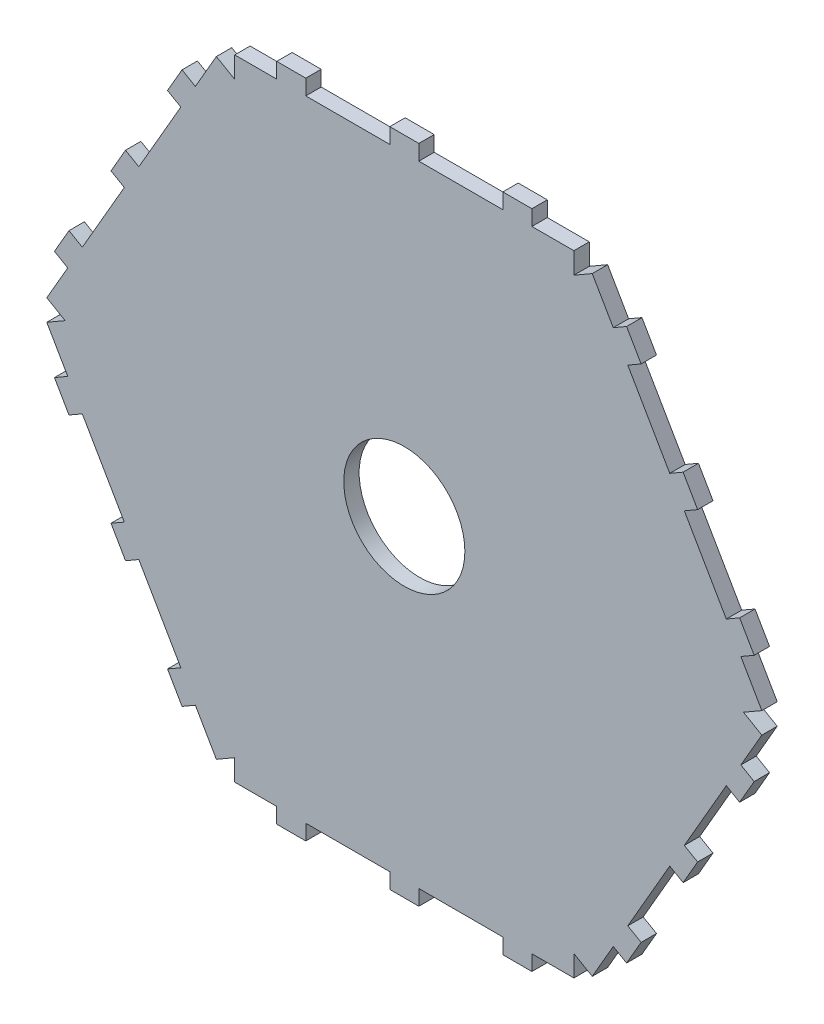
SolidWorks part; units mm, degrees
ref_plane "Front Plane" through (0, 0, 0) normal (0, 0, 1) x (1, 0, 0)
ref_plane "Top Plane" through (0, 0, 0) normal (0, 1, 0) x (1, 0, 0)
ref_plane "Right Plane" through (0, 0, 0) normal (1, 0, 0) x (0, 0, -1)
sketch "Sketch2" plane through (0, 0, 0) normal (0, 0, 1) x (1, 0, 0)
  line L0 (-35, 65) -> (-35, 60.6218)
  line L1 (35, 65) -> (35, 60.6218)
  line L2 (-35, 65) -> (-11.6667, 65) construction
  line L3 (-35, 60.6218) -> (35, 60.6218) construction
  line L4 (35, 60.6218) -> (70, 0) construction
  line L5 (70, 0) -> (35, -60.6218) construction
  line L6 (35, -60.6218) -> (-35, -60.6218) construction
  line L7 (0, 87.3633) -> (0, -0.0109) construction
  line L8 (0, 0) -> (44.1971, 0) construction
  line L9 (-11.6667, 65) -> (11.6667, 65) construction
  line L10 (11.6667, 65) -> (35, 65) construction
  line L11 (-23.3333, 65) -> (-23.3333, 68.175) construction
  line L12 (-20.3333, 68.175) -> (-26.3333, 68.175)
  line L13 (-35, -60.6218) -> (-70, 0) construction
  line L14 (-70, 0) -> (-35, 60.6218) construction
  line L15 (-70, 0) -> (59.0387, 0)
  line L16 (-26.3333, 68.175) -> (-26.3333, 65)
  line L17 (-26.3333, 68.175) -> (-20.3333, 68.175)
  line L18 (-20.3333, 68.175) -> (-20.3333, 65)
  line L19 (-11.6667, 137.7104) -> (-11.6667, 152.546) construction
  line L20 (11.6667, 137.7104) -> (11.6667, 152.546) construction
  line L21 (-26.3333, 68.175) -> (-26.3333, 65)
  line L22 (-20.3333, 68.175) -> (-20.3333, 65)
  line L23 (-26.3333, 68.175) -> (-26.3333, 65)
  line L24 (-20.3333, 68.175) -> (-20.3333, 65)
  line L25 (-26.3333, 68.175) -> (-26.3333, 65)
  line L26 (-20.3333, 68.175) -> (-20.3333, 65)
  line L27 (-26.3333, 68.175) -> (-26.3333, 65)
  line L28 (-20.3333, 68.175) -> (-20.3333, 65)
  line L29 (-26.3333, 68.175) -> (-26.3333, 65)
  line L30 (-20.3333, 68.175) -> (-20.3333, 65)
  line L31 (-26.3333, 68.175) -> (-26.3333, 65)
  line L32 (-20.3333, 68.175) -> (-20.3333, 65)
  line L33 (-26.3333, 68.175) -> (-26.3333, 65)
  line L34 (-20.3333, 68.175) -> (-20.3333, 65)
  line L35 (-26.3333, 68.175) -> (-26.3333, 65)
  line L36 (-20.3333, 68.175) -> (-20.3333, 65)
  line L37 (-26.3333, 68.175) -> (-26.3333, 65)
  line L38 (-20.3333, 68.175) -> (-20.3333, 65)
  line L39 (-26.3333, 68.175) -> (-26.3333, 65)
  line L40 (-20.3333, 68.175) -> (-20.3333, 65)
  line L41 (-26.3333, 68.175) -> (-26.3333, 65)
  line L42 (-20.3333, 68.175) -> (-20.3333, 65)
  line L43 (-26.3333, 68.175) -> (-26.3333, 65)
  line L44 (-20.3333, 68.175) -> (-20.3333, 65)
  line L45 (-26.3333, 68.175) -> (-26.3333, 65)
  line L46 (-20.3333, 68.175) -> (-20.3333, 65)
  line L47 (-26.3333, 68.175) -> (-26.3333, 65)
  line L48 (-20.3333, 68.175) -> (-20.3333, 65)
  line L49 (-26.3333, 68.175) -> (-26.3333, 65)
  line L50 (-20.3333, 68.175) -> (-20.3333, 65)
  line L51 (-26.3333, 68.175) -> (-26.3333, 65)
  line L52 (-20.3333, 68.175) -> (-20.3333, 65)
  line L53 (-26.3333, 68.175) -> (-26.3333, 65)
  line L54 (-20.3333, 68.175) -> (-20.3333, 65)
  line L55 (-26.3333, 68.175) -> (-26.3333, 65)
  line L56 (-20.3333, 68.175) -> (-20.3333, 65)
  line L57 (-26.3333, 68.175) -> (-26.3333, 65)
  line L58 (-20.3333, 68.175) -> (-20.3333, 65)
  line L59 (-26.3333, 68.175) -> (-26.3333, 65)
  line L60 (-20.3333, 68.175) -> (-20.3333, 65)
  line L61 (-26.3333, 68.175) -> (-26.3333, 65)
  line L62 (-20.3333, 68.175) -> (-20.3333, 65)
  line L63 (-26.3333, 68.175) -> (-26.3333, 65)
  line L64 (-20.3333, 68.175) -> (-20.3333, 65)
  line L65 (-26.3333, 68.175) -> (-26.3333, 65)
  line L66 (-20.3333, 68.175) -> (-20.3333, 65)
  line L67 (-26.3333, 68.175) -> (-26.3333, 65)
  line L68 (-20.3333, 68.175) -> (-20.3333, 65)
  line L69 (-26.3333, 68.175) -> (-26.3333, 65)
  line L70 (-20.3333, 68.175) -> (-20.3333, 65)
  line L71 (-26.3333, 68.175) -> (-26.3333, 65)
  line L72 (-20.3333, 68.175) -> (-20.3333, 65)
  line L73 (-26.3333, 68.175) -> (-26.3333, 65)
  line L74 (-20.3333, 68.175) -> (-20.3333, 65)
  line L75 (-26.3333, 68.175) -> (-26.3333, 65)
  line L76 (-20.3333, 68.175) -> (-20.3333, 65)
  line L77 (-26.3333, 68.175) -> (-26.3333, 65)
  line L78 (-20.3333, 68.175) -> (-20.3333, 65)
  line L79 (-26.3333, 68.175) -> (-26.3333, 65)
  line L80 (-20.3333, 68.175) -> (-20.3333, 65)
  line L81 (-26.3333, 68.175) -> (-26.3333, 65)
  line L82 (-20.3333, 68.175) -> (-20.3333, 65)
  line L83 (0, 65) -> (0, 68.175) construction
  line L84 (-3, 68.175) -> (-3, 65)
  line L85 (3, 68.175) -> (3, 65)
  line L86 (-3, 68.175) -> (-3, 65)
  line L87 (3, 68.175) -> (3, 65)
  line L88 (-3, 68.175) -> (-3, 65)
  line L89 (3, 68.175) -> (3, 65)
  line L90 (-3, 68.175) -> (-3, 65)
  line L91 (3, 68.175) -> (3, 65)
  line L92 (-3, 68.175) -> (-3, 65)
  line L93 (3, 68.175) -> (3, 65)
  line L94 (-3, 68.175) -> (-3, 65)
  line L95 (3, 68.175) -> (3, 65)
  line L96 (-3, 68.175) -> (-3, 65)
  line L97 (3, 68.175) -> (3, 65)
  line L98 (-3, 68.175) -> (-3, 65)
  line L99 (3, 68.175) -> (3, 65)
  line L100 (-3, 68.175) -> (-3, 65)
  line L101 (3, 68.175) -> (3, 65)
  line L102 (-3, 68.175) -> (-3, 65)
  line L103 (3, 68.175) -> (3, 65)
  line L104 (-3, 68.175) -> (-3, 65)
  line L105 (3, 68.175) -> (3, 65)
  line L106 (-3, 68.175) -> (-3, 65)
  line L107 (3, 68.175) -> (3, 65)
  line L108 (-3, 68.175) -> (-3, 65)
  line L109 (3, 68.175) -> (3, 65)
  line L110 (-3, 68.175) -> (-3, 65)
  line L111 (3, 68.175) -> (3, 65)
  line L112 (-3, 68.175) -> (-3, 65)
  line L113 (3, 68.175) -> (3, 65)
  line L114 (-3, 68.175) -> (-3, 65)
  line L115 (3, 68.175) -> (3, 65)
  line L116 (-3, 68.175) -> (-3, 65)
  line L117 (3, 68.175) -> (3, 65)
  line L118 (-3, 68.175) -> (-3, 65)
  line L119 (3, 68.175) -> (3, 65)
  line L120 (-3, 68.175) -> (-3, 65)
  line L121 (3, 68.175) -> (3, 65)
  line L122 (-3, 68.175) -> (-3, 65)
  line L123 (3, 68.175) -> (3, 65)
  line L124 (-3, 68.175) -> (-3, 65)
  line L125 (3, 68.175) -> (3, 65)
  line L126 (-3, 68.175) -> (-3, 65)
  line L127 (3, 68.175) -> (3, 65)
  line L128 (-3, 68.175) -> (-3, 65)
  line L129 (3, 68.175) -> (3, 65)
  line L130 (-3, 68.175) -> (-3, 65)
  line L131 (3, 68.175) -> (3, 65)
  line L132 (-3, 68.175) -> (-3, 65)
  line L133 (3, 68.175) -> (3, 65)
  line L134 (-3, 68.175) -> (-3, 65)
  line L135 (3, 68.175) -> (3, 65)
  line L136 (-3, 68.175) -> (-3, 65)
  line L137 (3, 68.175) -> (3, 65)
  line L138 (-3, 68.175) -> (-3, 65)
  line L139 (3, 68.175) -> (3, 65)
  line L140 (-3, 68.175) -> (-3, 65)
  line L141 (3, 68.175) -> (3, 65)
  line L142 (-3, 68.175) -> (-3, 65)
  line L143 (3, 68.175) -> (3, 65)
  line L144 (-3, 68.175) -> (-3, 65)
  line L145 (3, 68.175) -> (3, 65)
  line L146 (-3, 68.175) -> (-3, 65)
  line L147 (3, 68.175) -> (-3, 68.175)
  line L148 (3, 68.175) -> (3, 65)
  line L149 (-3, 68.175) -> (3, 68.175)
  line L150 (-3, 68.175) -> (-3, 65)
  line L151 (3, 68.175) -> (3, 65)
  line L152 (-3, 68.175) -> (-3, 65)
  line L153 (3, 68.175) -> (3, 65)
  line L154 (-3, 68.175) -> (-3, 65)
  line L155 (3, 68.175) -> (3, 65)
  line L156 (-3, 68.175) -> (-3, 65)
  line L157 (3, 68.175) -> (3, 65)
  line L158 (-3, 68.175) -> (-3, 65)
  line L159 (3, 68.175) -> (3, 65)
  line L160 (-3, 68.175) -> (-3, 65)
  line L161 (3, 68.175) -> (3, 65)
  line L162 (-3, 68.175) -> (-3, 65)
  line L163 (3, 68.175) -> (3, 65)
  line L164 (-3, 68.175) -> (-3, 65)
  line L165 (3, 68.175) -> (3, 65)
  line L166 (-3, 68.175) -> (-3, 65)
  line L167 (3, 68.175) -> (3, 65)
  line L168 (-3, 68.175) -> (-3, 65)
  line L169 (3, 68.175) -> (3, 65)
  line L170 (-3, 68.175) -> (-3, 65)
  line L171 (3, 68.175) -> (3, 65)
  line L172 (-3, 68.175) -> (-3, 65)
  line L173 (3, 68.175) -> (3, 65)
  line L174 (-3, 68.175) -> (-3, 65)
  line L175 (3, 68.175) -> (3, 65)
  line L176 (-3, 68.175) -> (-3, 65)
  line L177 (3, 68.175) -> (3, 65)
  line L178 (-3, 68.175) -> (-3, 65)
  line L179 (3, 68.175) -> (3, 65)
  line L180 (-3, 68.175) -> (-3, 65)
  line L181 (3, 68.175) -> (3, 65)
  line L182 (-3, 68.175) -> (-3, 65)
  line L183 (3, 68.175) -> (3, 65)
  line L184 (-3, 68.175) -> (-3, 65)
  line L185 (3, 68.175) -> (3, 65)
  line L186 (-3, 68.175) -> (-3, 65)
  line L187 (3, 68.175) -> (3, 65)
  line L188 (-3, 68.175) -> (-3, 65)
  line L189 (3, 68.175) -> (3, 65)
  line L190 (-3, 68.175) -> (-3, 65)
  line L191 (3, 68.175) -> (3, 65)
  line L192 (-3, 68.175) -> (-3, 65)
  line L193 (3, 68.175) -> (3, 65)
  line L194 (-3, 68.175) -> (-3, 65)
  line L195 (3, 68.175) -> (3, 65)
  line L196 (-3, 68.175) -> (-3, 65)
  line L197 (3, 68.175) -> (3, 65)
  line L198 (-3, 68.175) -> (-3, 65)
  line L199 (3, 68.175) -> (3, 65)
  line L200 (-3, 68.175) -> (-3, 65)
  line L201 (3, 68.175) -> (3, 65)
  line L202 (-3, 68.175) -> (-3, 65)
  line L203 (3, 68.175) -> (3, 65)
  line L204 (-3, 68.175) -> (-3, 65)
  line L205 (3, 68.175) -> (3, 65)
  line L206 (-3, 68.175) -> (-3, 65)
  line L207 (3, 68.175) -> (3, 65)
  line L208 (-3, 68.175) -> (-3, 65)
  line L209 (3, 68.175) -> (3, 65)
  line L210 (-3, 68.175) -> (-3, 65)
  line L211 (3, 68.175) -> (3, 65)
  line L212 (-3, 68.175) -> (-3, 65)
  line L213 (3, 68.175) -> (3, 65)
  line L214 (23.3333, 65) -> (23.3333, 68.175) construction
  line L215 (20.3333, 68.175) -> (20.3333, 65)
  line L216 (26.3333, 68.175) -> (26.3333, 65)
  line L217 (20.3333, 68.175) -> (20.3333, 65)
  line L218 (26.3333, 68.175) -> (26.3333, 65)
  line L219 (20.3333, 68.175) -> (20.3333, 65)
  line L220 (26.3333, 68.175) -> (26.3333, 65)
  line L221 (20.3333, 68.175) -> (20.3333, 65)
  line L222 (26.3333, 68.175) -> (26.3333, 65)
  line L223 (20.3333, 68.175) -> (20.3333, 65)
  line L224 (26.3333, 68.175) -> (26.3333, 65)
  line L225 (20.3333, 68.175) -> (20.3333, 65)
  line L226 (26.3333, 68.175) -> (26.3333, 65)
  line L227 (20.3333, 68.175) -> (20.3333, 65)
  line L228 (26.3333, 68.175) -> (26.3333, 65)
  line L229 (20.3333, 68.175) -> (20.3333, 65)
  line L230 (26.3333, 68.175) -> (26.3333, 65)
  line L231 (20.3333, 68.175) -> (20.3333, 65)
  line L232 (26.3333, 68.175) -> (26.3333, 65)
  line L233 (20.3333, 68.175) -> (20.3333, 65)
  line L234 (26.3333, 68.175) -> (26.3333, 65)
  line L235 (20.3333, 68.175) -> (20.3333, 65)
  line L236 (26.3333, 68.175) -> (26.3333, 65)
  line L237 (20.3333, 68.175) -> (20.3333, 65)
  line L238 (26.3333, 68.175) -> (26.3333, 65)
  line L239 (20.3333, 68.175) -> (20.3333, 65)
  line L240 (26.3333, 68.175) -> (26.3333, 65)
  line L241 (20.3333, 68.175) -> (20.3333, 65)
  line L242 (26.3333, 68.175) -> (26.3333, 65)
  line L243 (20.3333, 68.175) -> (20.3333, 65)
  line L244 (26.3333, 68.175) -> (26.3333, 65)
  line L245 (20.3333, 68.175) -> (20.3333, 65)
  line L246 (26.3333, 68.175) -> (26.3333, 65)
  line L247 (20.3333, 68.175) -> (20.3333, 65)
  line L248 (26.3333, 68.175) -> (26.3333, 65)
  line L249 (20.3333, 68.175) -> (20.3333, 65)
  line L250 (26.3333, 68.175) -> (26.3333, 65)
  line L251 (20.3333, 68.175) -> (20.3333, 65)
  line L252 (26.3333, 68.175) -> (26.3333, 65)
  line L253 (20.3333, 68.175) -> (20.3333, 65)
  line L254 (26.3333, 68.175) -> (26.3333, 65)
  line L255 (20.3333, 68.175) -> (20.3333, 65)
  line L256 (26.3333, 68.175) -> (26.3333, 65)
  line L257 (20.3333, 68.175) -> (20.3333, 65)
  line L258 (26.3333, 68.175) -> (26.3333, 65)
  line L259 (20.3333, 68.175) -> (20.3333, 65)
  line L260 (26.3333, 68.175) -> (26.3333, 65)
  line L261 (20.3333, 68.175) -> (20.3333, 65)
  line L262 (26.3333, 68.175) -> (26.3333, 65)
  line L263 (20.3333, 68.175) -> (20.3333, 65)
  line L264 (26.3333, 68.175) -> (26.3333, 65)
  line L265 (20.3333, 68.175) -> (20.3333, 65)
  line L266 (26.3333, 68.175) -> (26.3333, 65)
  line L267 (20.3333, 68.175) -> (20.3333, 65)
  line L268 (26.3333, 68.175) -> (26.3333, 65)
  line L269 (20.3333, 68.175) -> (20.3333, 65)
  line L270 (26.3333, 68.175) -> (26.3333, 65)
  line L271 (20.3333, 68.175) -> (20.3333, 65)
  line L272 (26.3333, 68.175) -> (26.3333, 65)
  line L273 (20.3333, 68.175) -> (20.3333, 65)
  line L274 (26.3333, 68.175) -> (26.3333, 65)
  line L275 (20.3333, 68.175) -> (20.3333, 65)
  line L276 (26.3333, 68.175) -> (26.3333, 65)
  line L277 (20.3333, 68.175) -> (20.3333, 65)
  line L278 (26.3333, 68.175) -> (26.3333, 65)
  line L279 (26.3333, 68.175) -> (20.3333, 68.175)
  line L280 (20.3333, 68.175) -> (20.3333, 65)
  line L281 (20.3333, 68.175) -> (26.3333, 68.175)
  line L282 (26.3333, 68.175) -> (26.3333, 65)
  line L283 (20.3333, 68.175) -> (20.3333, 65)
  line L284 (26.3333, 68.175) -> (26.3333, 65)
  line L285 (20.3333, 68.175) -> (20.3333, 65)
  line L286 (26.3333, 68.175) -> (26.3333, 65)
  line L287 (20.3333, 68.175) -> (20.3333, 65)
  line L288 (26.3333, 68.175) -> (26.3333, 65)
  line L289 (20.3333, 68.175) -> (20.3333, 65)
  line L290 (26.3333, 68.175) -> (26.3333, 65)
  line L291 (20.3333, 68.175) -> (20.3333, 65)
  line L292 (26.3333, 68.175) -> (26.3333, 65)
  line L293 (20.3333, 68.175) -> (20.3333, 65)
  line L294 (26.3333, 68.175) -> (26.3333, 65)
  line L295 (20.3333, 68.175) -> (20.3333, 65)
  line L296 (26.3333, 68.175) -> (26.3333, 65)
  line L297 (20.3333, 68.175) -> (20.3333, 65)
  line L298 (26.3333, 68.175) -> (26.3333, 65)
  line L299 (20.3333, 68.175) -> (20.3333, 65)
  line L300 (26.3333, 68.175) -> (26.3333, 65)
  line L301 (20.3333, 68.175) -> (20.3333, 65)
  line L302 (26.3333, 68.175) -> (26.3333, 65)
  line L303 (20.3333, 68.175) -> (20.3333, 65)
  line L304 (26.3333, 68.175) -> (26.3333, 65)
  line L305 (20.3333, 68.175) -> (20.3333, 65)
  line L306 (26.3333, 68.175) -> (26.3333, 65)
  line L307 (20.3333, 68.175) -> (20.3333, 65)
  line L308 (26.3333, 68.175) -> (26.3333, 65)
  line L309 (20.3333, 68.175) -> (20.3333, 65)
  line L310 (26.3333, 68.175) -> (26.3333, 65)
  line L311 (20.3333, 68.175) -> (20.3333, 65)
  line L312 (26.3333, 68.175) -> (26.3333, 65)
  line L313 (20.3333, 68.175) -> (20.3333, 65)
  line L314 (26.3333, 68.175) -> (26.3333, 65)
  line L315 (20.3333, 68.175) -> (20.3333, 65)
  line L316 (26.3333, 68.175) -> (26.3333, 65)
  line L317 (20.3333, 68.175) -> (20.3333, 65)
  line L318 (26.3333, 68.175) -> (26.3333, 65)
  line L319 (20.3333, 68.175) -> (20.3333, 65)
  line L320 (26.3333, 68.175) -> (26.3333, 65)
  line L321 (20.3333, 68.175) -> (20.3333, 65)
  line L322 (26.3333, 68.175) -> (26.3333, 65)
  line L323 (20.3333, 68.175) -> (20.3333, 65)
  line L324 (26.3333, 68.175) -> (26.3333, 65)
  line L325 (20.3333, 68.175) -> (20.3333, 65)
  line L326 (26.3333, 68.175) -> (26.3333, 65)
  line L327 (20.3333, 68.175) -> (20.3333, 65)
  line L328 (26.3333, 68.175) -> (26.3333, 65)
  line L329 (20.3333, 68.175) -> (20.3333, 65)
  line L330 (26.3333, 68.175) -> (26.3333, 65)
  line L331 (20.3333, 68.175) -> (20.3333, 65)
  line L332 (26.3333, 68.175) -> (26.3333, 65)
  line L333 (20.3333, 68.175) -> (20.3333, 65)
  line L334 (26.3333, 68.175) -> (26.3333, 65)
  line L335 (20.3333, 68.175) -> (20.3333, 65)
  line L336 (26.3333, 68.175) -> (26.3333, 65)
  line L337 (20.3333, 68.175) -> (20.3333, 65)
  line L338 (26.3333, 68.175) -> (26.3333, 65)
  line L339 (20.3333, 68.175) -> (20.3333, 65)
  line L340 (26.3333, 68.175) -> (26.3333, 65)
  line L341 (20.3333, 68.175) -> (20.3333, 65)
  line L342 (26.3333, 68.175) -> (26.3333, 65)
  line L343 (20.3333, 68.175) -> (20.3333, 65)
  line L344 (26.3333, 68.175) -> (26.3333, 65)
  line L345 (-35, 65) -> (-26.3333, 65)
  line L346 (-20.3333, 65) -> (-3, 65)
  line L347 (3, 65) -> (20.3333, 65)
  line L348 (26.3333, 65) -> (35, 65)
  line L349 (45.8746, 56.8928) -> (43.125, 55.3053)
  line L350 (48.8746, 51.6967) -> (45.8746, 56.8928)
  line L351 (48.8746, 51.6967) -> (46.125, 50.1092)
  line L352 (46.125, 50.1092) -> (54.7917, 35.0981)
  line L353 (57.5413, 36.6856) -> (54.7917, 35.0981)
  line L354 (60.5413, 31.4894) -> (57.5413, 36.6856)
  line L355 (60.5413, 31.4894) -> (57.7917, 29.9019)
  line L356 (57.7917, 29.9019) -> (66.4583, 14.8908)
  line L357 (69.2079, 16.4783) -> (66.4583, 14.8908)
  line L358 (72.2079, 11.2822) -> (69.2079, 16.4783)
  line L359 (72.2079, 11.2822) -> (69.4583, 9.6947)
  line L360 (69.4583, 9.6947) -> (73.7917, 2.1891)
  line L361 (38.7917, 62.8109) -> (43.125, 55.3053)
  line L362 (38.7917, 62.8109) -> (35, 60.6218)
  line L363 (73.7917, 2.1891) -> (70, 0)
  line L364 (72.2079, -11.2822) -> (69.4583, -9.6947)
  line L365 (69.2079, -16.4783) -> (72.2079, -11.2822)
  line L366 (69.2079, -16.4783) -> (66.4583, -14.8908)
  line L367 (66.4583, -14.8908) -> (57.7917, -29.9019)
  line L368 (60.5413, -31.4894) -> (57.7917, -29.9019)
  line L369 (57.5413, -36.6856) -> (60.5413, -31.4894)
  line L370 (57.5413, -36.6856) -> (54.7917, -35.0981)
  line L371 (54.7917, -35.0981) -> (46.125, -50.1092)
  line L372 (48.8746, -51.6967) -> (46.125, -50.1092)
  line L373 (45.8746, -56.8928) -> (48.8746, -51.6967)
  line L374 (45.8746, -56.8928) -> (43.125, -55.3053)
  line L375 (43.125, -55.3053) -> (38.7917, -62.8109)
  line L376 (73.7917, -2.1891) -> (69.4583, -9.6947)
  line L377 (73.7917, -2.1891) -> (70, 0)
  line L378 (38.7917, -62.8109) -> (35, -60.6218)
  line L379 (26.3333, -68.175) -> (26.3333, -65)
  line L380 (20.3333, -68.175) -> (26.3333, -68.175)
  line L381 (20.3333, -68.175) -> (20.3333, -65)
  line L382 (20.3333, -65) -> (3, -65)
  line L383 (3, -68.175) -> (3, -65)
  line L384 (-3, -68.175) -> (3, -68.175)
  line L385 (-3, -68.175) -> (-3, -65)
  line L386 (-3, -65) -> (-20.3333, -65)
  line L387 (-20.3333, -68.175) -> (-20.3333, -65)
  line L388 (-26.3333, -68.175) -> (-20.3333, -68.175)
  line L389 (-26.3333, -68.175) -> (-26.3333, -65)
  line L390 (-26.3333, -65) -> (-35, -65)
  line L391 (35, -65) -> (26.3333, -65)
  line L392 (35, -65) -> (35, -60.6218)
  line L393 (-35, -65) -> (-35, -60.6218)
  line L394 (-45.8746, -56.8928) -> (-43.125, -55.3053)
  line L395 (-48.8746, -51.6967) -> (-45.8746, -56.8928)
  line L396 (-48.8746, -51.6967) -> (-46.125, -50.1092)
  line L397 (-46.125, -50.1092) -> (-54.7917, -35.0981)
  line L398 (-57.5413, -36.6856) -> (-54.7917, -35.0981)
  line L399 (-60.5413, -31.4894) -> (-57.5413, -36.6856)
  line L400 (-60.5413, -31.4894) -> (-57.7917, -29.9019)
  line L401 (-57.7917, -29.9019) -> (-66.4583, -14.8908)
  line L402 (-69.2079, -16.4783) -> (-66.4583, -14.8908)
  line L403 (-72.2079, -11.2822) -> (-69.2079, -16.4783)
  line L404 (-72.2079, -11.2822) -> (-69.4583, -9.6947)
  line L405 (-69.4583, -9.6947) -> (-73.7917, -2.1891)
  line L406 (-38.7917, -62.8109) -> (-43.125, -55.3053)
  line L407 (-38.7917, -62.8109) -> (-35, -60.6218)
  line L408 (-73.7917, -2.1891) -> (-70, 0)
  line L409 (-72.2079, 11.2822) -> (-69.4583, 9.6947)
  line L410 (-69.2079, 16.4783) -> (-72.2079, 11.2822)
  line L411 (-69.2079, 16.4783) -> (-66.4583, 14.8908)
  line L412 (-66.4583, 14.8908) -> (-57.7917, 29.9019)
  line L413 (-60.5413, 31.4894) -> (-57.7917, 29.9019)
  line L414 (-57.5413, 36.6856) -> (-60.5413, 31.4894)
  line L415 (-57.5413, 36.6856) -> (-54.7917, 35.0981)
  line L416 (-54.7917, 35.0981) -> (-46.125, 50.1092)
  line L417 (-48.8746, 51.6967) -> (-46.125, 50.1092)
  line L418 (-45.8746, 56.8928) -> (-48.8746, 51.6967)
  line L419 (-45.8746, 56.8928) -> (-43.125, 55.3053)
  line L420 (-43.125, 55.3053) -> (-38.7917, 62.8109)
  line L421 (-73.7917, 2.1891) -> (-69.4583, 9.6947)
  line L422 (-73.7917, 2.1891) -> (-70, 0)
  line L423 (-38.7917, 62.8109) -> (-35, 60.6218)
  circle A0 centre (0, 0) radius 12.5
  point P121 (0, 0)
  dimension "D7" = 25
  dimension "D1" = 70
  dimension "D2" = 6
  dimension "D3" = 6
  dimension "D4" = 3.175
  dimension "D5" = 120
  dimension "D6" = 130
extrude "Boss-Extrude1" add sketch "Sketch2" along normal mid plane 3.175
